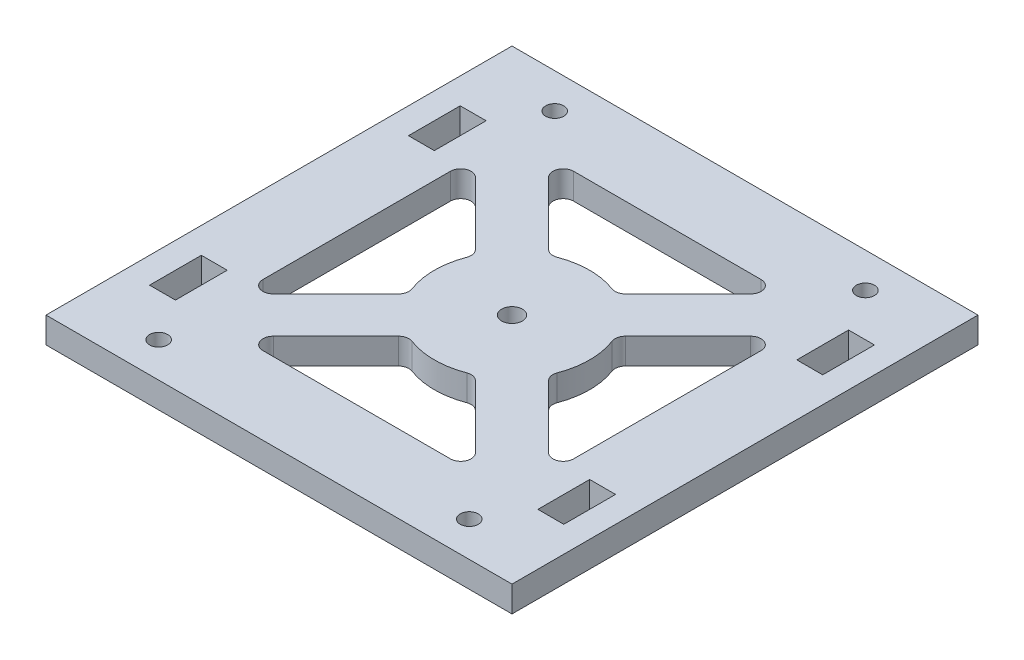
SolidWorks part; units mm, degrees
ref_plane "Front Plane" through (0, 0, 0) normal (0, 0, 1) x (1, 0, 0)
ref_plane "Top Plane" through (0, 0, 0) normal (0, 1, 0) x (1, 0, 0)
ref_plane "Right Plane" through (0, 0, 0) normal (1, 0, 0) x (0, 0, -1)
sketch "Sketch1" plane through (0, 0, 0) normal (0, 1, 0) x (1, 0, 0)
  line L0 (-26.5858, 19.5147) -> (-14.49, 7.4189)
  line L5 (-45, 45) -> (45, 45)
  line L6 (-45, 45) -> (-45, -45)
  line L11 (-45, -45) -> (45, -45)
  line L20 (45, 45) -> (45, -45)
  line L21 (-45, 45) -> (45, -45) construction
  line L23 (-45, -45) -> (45, 45) construction
  line L55 (-18.1005, 30) -> (18.1005, 30)
  line L60 (-30, 18.1005) -> (-30, -18.1005)
  line L61 (-30, -30) -> (0, -30) construction
  line L62 (30, 0) -> (30, -30) construction
  line L63 (-30, 30) -> (30, -30) construction
  line L64 (-30, -30) -> (30, 30) construction
  line L65 (-19.5147, 26.5858) -> (-7.4189, 14.49)
  line L66 (-30, 30) -> (-30, 22.9289) construction
  line L67 (-30, 30) -> (-22.9289, 30) construction
  line L68 (-1000, 0) -> (49000, 0) construction
  line L69 (0, -1000) -> (0, 49000) construction
  line L70 (0, 30) -> (30, 30) construction
  line L71 (30, 30) -> (30, -30) construction
  line L72 (0, -30) -> (30, -30) construction
  line L73 (-30, 0) -> (-30, -30) construction
  line L74 (30, 30) -> (22.9289, 30) construction
  line L75 (30, 30) -> (30, 22.9289) construction
  line L76 (19.5147, 26.5858) -> (7.4189, 14.49)
  line L77 (30, 18.1005) -> (30, -18.1005)
  line L78 (26.5858, 19.5147) -> (14.49, 7.4189)
  line L79 (30, -30) -> (30, -22.9289) construction
  line L80 (30, -30) -> (22.9289, -30) construction
  line L81 (0, -30) -> (30, -30) construction
  line L82 (-30, -30) -> (-22.9289, -30) construction
  line L83 (-30, -30) -> (-30, -22.9289) construction
  line L84 (26.5858, -19.5147) -> (14.49, -7.4189)
  line L85 (19.5147, -26.5858) -> (7.4189, -14.49)
  line L86 (-19.5147, -26.5858) -> (-7.4189, -14.49)
  line L87 (-18.1005, -30) -> (18.1005, -30)
  line L88 (-26.5858, -19.5147) -> (-14.49, -7.4189)
  circle A0 centre (0, 0) radius 2
  arc A1 (-14.0331, 5.2983) -> (-14.0331, -5.2983) centre (0, 0) ccw
  arc A2 (-6.4645, 13.5355) -> (-10.6066, 10.6066) centre (0, 0) ccw construction
  arc A3 (-10.6066, 10.6066) -> (-13.5355, 6.4645) centre (0, 0) ccw construction
  arc A4 (-5.2983, 14.0331) -> (-7.4189, 14.49) centre (-6.0047, 15.9042) cw
  arc A5 (-14.0331, 5.2983) -> (-14.49, 7.4189) centre (-15.9042, 6.0047) ccw
  arc A6 (-26.5858, 19.5147) -> (-30, 18.1005) centre (-28, 18.1005) ccw
  arc A7 (-18.1005, 30) -> (-19.5147, 26.5858) centre (-18.1005, 28) ccw
  arc A8 (-15, 0) -> (-10.6066, -10.6066) centre (0, 0) ccw construction
  arc A9 (5.2983, 14.0331) -> (-5.2983, 14.0331) centre (0, 0) ccw
  arc A10 (-10.6066, -10.6066) -> (0, -15) centre (0, 0) ccw construction
  arc A11 (0, -15) -> (10.6066, -10.6066) centre (0, 0) ccw construction
  arc A12 (10.6066, -10.6066) -> (15, 0) centre (0, 0) ccw construction
  arc A13 (10.6066, -10.6066) -> (10.6066, 10.6066) centre (0, 0) ccw construction
  arc A14 (10.6066, 10.6066) -> (0, 15) centre (0, 0) ccw construction
  arc A15 (10.6066, 10.6066) -> (13.5355, 6.4645) centre (0, 0) cw construction
  arc A16 (6.4645, 13.5355) -> (10.6066, 10.6066) centre (0, 0) cw construction
  arc A17 (18.1005, 30) -> (19.5147, 26.5858) centre (18.1005, 28) cw
  arc A18 (26.5858, 19.5147) -> (30, 18.1005) centre (28, 18.1005) cw
  arc A19 (14.0331, 5.2983) -> (14.49, 7.4189) centre (15.9042, 6.0047) cw
  arc A20 (5.2983, 14.0331) -> (7.4189, 14.49) centre (6.0047, 15.9042) ccw
  arc A21 (14.0331, 5.2983) -> (14.0331, -5.2983) centre (0, 0) cw
  arc A22 (6.4645, -13.5355) -> (10.6066, -10.6066) centre (0, 0) ccw construction
  arc A23 (10.6066, -10.6066) -> (13.5355, -6.4645) centre (0, 0) ccw construction
  arc A24 (10.6066, -10.6066) -> (0, -15) centre (0, 0) cw construction
  arc A25 (-10.6066, -10.6066) -> (-13.5355, -6.4645) centre (0, 0) cw construction
  arc A26 (-6.4645, -13.5355) -> (-10.6066, -10.6066) centre (0, 0) cw construction
  arc A27 (5.2983, -14.0331) -> (7.4189, -14.49) centre (6.0047, -15.9042) cw
  arc A28 (14.0331, -5.2983) -> (14.49, -7.4189) centre (15.9042, -6.0047) ccw
  arc A29 (26.5858, -19.5147) -> (30, -18.1005) centre (28, -18.1005) ccw
  arc A30 (18.1005, -30) -> (19.5147, -26.5858) centre (18.1005, -28) ccw
  arc A31 (5.2983, -14.0331) -> (-5.2983, -14.0331) centre (0, 0) cw
  arc A32 (-18.1005, -30) -> (-19.5147, -26.5858) centre (-18.1005, -28) cw
  arc A33 (-26.5858, -19.5147) -> (-30, -18.1005) centre (-28, -18.1005) cw
  arc A34 (-14.0331, -5.2983) -> (-14.49, -7.4189) centre (-15.9042, -6.0047) cw
  arc A35 (-5.2983, -14.0331) -> (-7.4189, -14.49) centre (-6.0047, -15.9042) ccw
  point P0 (0, 0)
  dimension "D3" = 30
  dimension "D4" = 4
  dimension "D8" = 2
  dimension "D1" = 90
  dimension "D2" = 90
  dimension "D5" = 15
  dimension "D6" = 15
  dimension "D7" = 5
extrude "Boss-Extrude1" add sketch "Sketch1" along normal blind 5
sketch "Sketch2" plane through (0, 5, 0) normal (0, 1, 0) x (1, 0, 0)
  line L0 (-998.1413, -40) -> (49001.8587, -40) construction
  line L1 (0, -1000) -> (0, 49000) construction
  line L2 (-1000, 0) -> (49000, 0) construction
  line L3 (-45, -45) -> (45, -45) construction
  line L4 (40, 30) -> (35, 30)
  line L5 (-40, -1027.013) -> (-40, 48972.987) construction
  line L6 (-45, 45) -> (-45, -45) construction
  line L7 (35, -30) -> (35, -20)
  line L8 (-40, -30) -> (-35, -30)
  line L9 (-40, -30) -> (-40, -20)
  line L10 (-40, -20) -> (-35, -20)
  line L11 (-35, -30) -> (-35, -20)
  line L12 (40, -20) -> (35, -20)
  line L13 (40, -30) -> (40, -20)
  line L14 (40, -30) -> (35, -30)
  line L15 (40, 30) -> (40, 20)
  line L16 (40, 20) -> (35, 20)
  line L17 (35, 30) -> (35, 20)
  line L18 (-35, 30) -> (-35, 20)
  line L19 (-40, 20) -> (-35, 20)
  line L20 (-40, 30) -> (-40, 20)
  line L21 (-40, 30) -> (-35, 30)
  circle A0 centre (-30, -38.25) radius 1.75
  circle A1 centre (30, -38.25) radius 1.75
  circle A2 centre (30, 38.25) radius 1.75
  circle A3 centre (-30, 38.25) radius 1.75
  dimension "D2" = 3.5
  dimension "D1" = 5
  dimension "D3" = 30
  dimension "D4" = 5
  dimension "D5" = 20
  dimension "D6" = 5
  dimension "D7" = 10
extrude "Cut-Extrude1" cut sketch "Sketch2" against normal through all both and the other way through all
